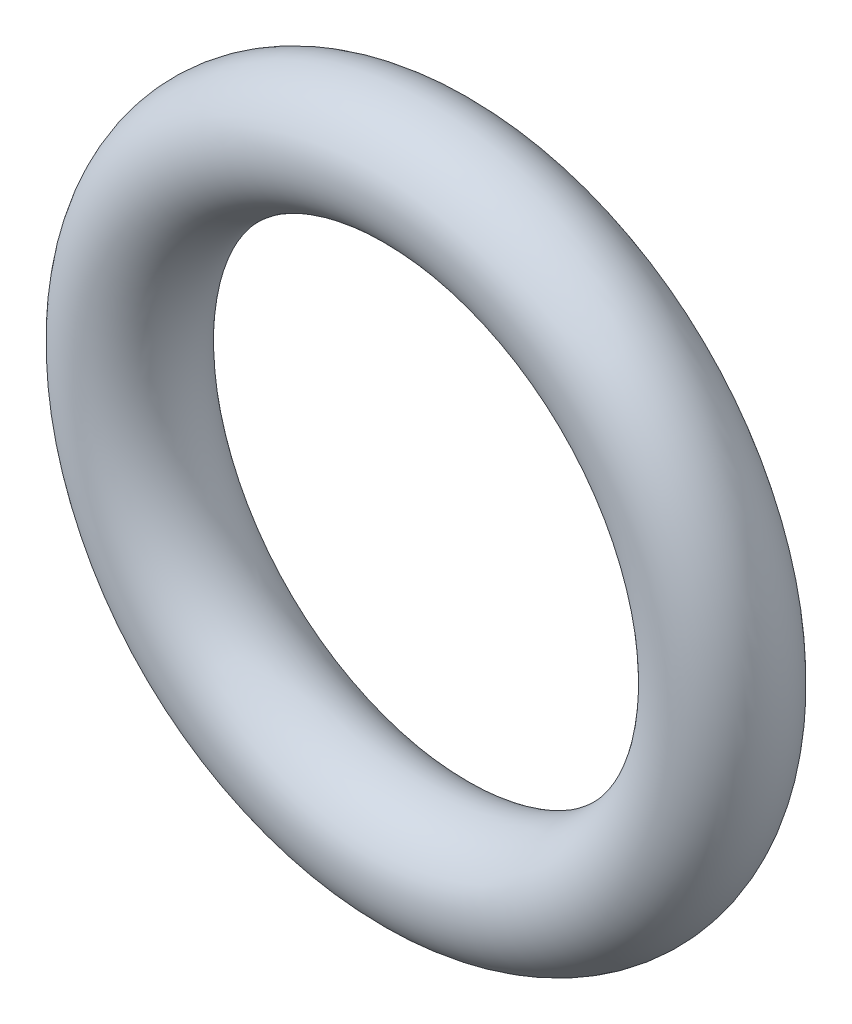
SolidWorks part; units mm, degrees
ref_plane "Front Plane" through (0, 0, 0) normal (0, 0, 1) x (1, 0, 0)
ref_plane "Top Plane" through (0, 0, 0) normal (0, 1, 0) x (1, 0, 0)
ref_plane "Right Plane" through (0, 0, 0) normal (1, 0, 0) x (0, 0, -1)
sketch "Sketch1" plane through (0, 0, 0) normal (1, 0, 0) x (0, 0, -1)
  circle A0 centre (0, 0) radius 1.6867
  dimension "D1" = 3.3734
sketch "Sketch2" plane through (0, 0, 0) normal (0, 0, 1) x (1, 0, 0)
  circle A0 centre (0, -8.4336) radius 8.4336
  dimension "D1" = 16.8672
sweep "Sweep1" add profiles "Sketch1" path "Sketch2"
ref_point "Point1" parameters "D1"=0.762
sketch "Sketch3" plane through (0, 0, 0) normal (0, 0, 1) x (1, 0, 0)
  line L0 (0, -1.6867) -> (0, -15.1805) construction
  circle A0 centre (0, -8.4336) radius 6.7469 construction
  circle A1 centre (0, -8.4336) radius 6.7469
  point P3 (-4.7625, -3.6546)
  point P4 (4.7625, -3.6546)
  point P5 (4.7625, -13.2126)
  point P6 (-4.7625, -13.2126)
  dimension "D1" = 9.525
  dimension "D2" = 9.525
ref_point "Point2"
ref_point "Point3"
ref_point "Point4"
ref_point "Point5"
sketch "Sketch4" plane through (0, 0, 0) normal (1, 0, 0) x (0, 0, -1)
  point P0 (1.6294, -17.2048)
ref_point "Point6"
ref_plane "Plane1" through (0, -15.113, 0) normal (0, 1, 0) x (1, 0, 0)
